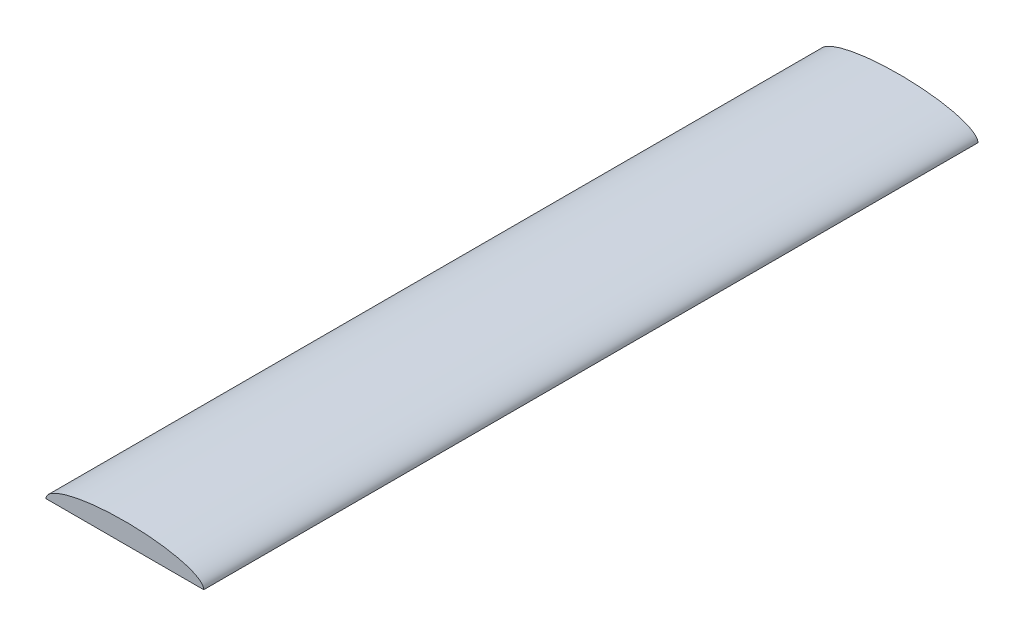
SolidWorks part; units mm, degrees
ref_plane "Front Plane" through (0, 0, 0) normal (0, 0, 1) x (1, 0, 0)
ref_plane "Top Plane" through (0, 0, 0) normal (0, 1, 0) x (1, 0, 0)
ref_plane "Right Plane" through (0, 0, 0) normal (1, 0, 0) x (0, 0, -1)
sketch "Sketch1" plane through (0, 0, 0) normal (0, 0, 1) x (1, 0, 0)
  line L0 (0, 0) -> (0, 0.6565) construction
  line L1 (0, 0) -> (1.4528, 0) construction
  line L2 (-2.516, 0) -> (2.516, 0)
  ellipse E0 centre (0, 0) end of major axis (2.516, 0) minor radius 0.635 (2.516, 0) -> (-2.516, 0) ccw
  dimension "D1" = 0.635
  dimension "D2" = 2.516
extrude "Boss-Extrude1" add sketch "Sketch1" along normal mid plane 24.7
